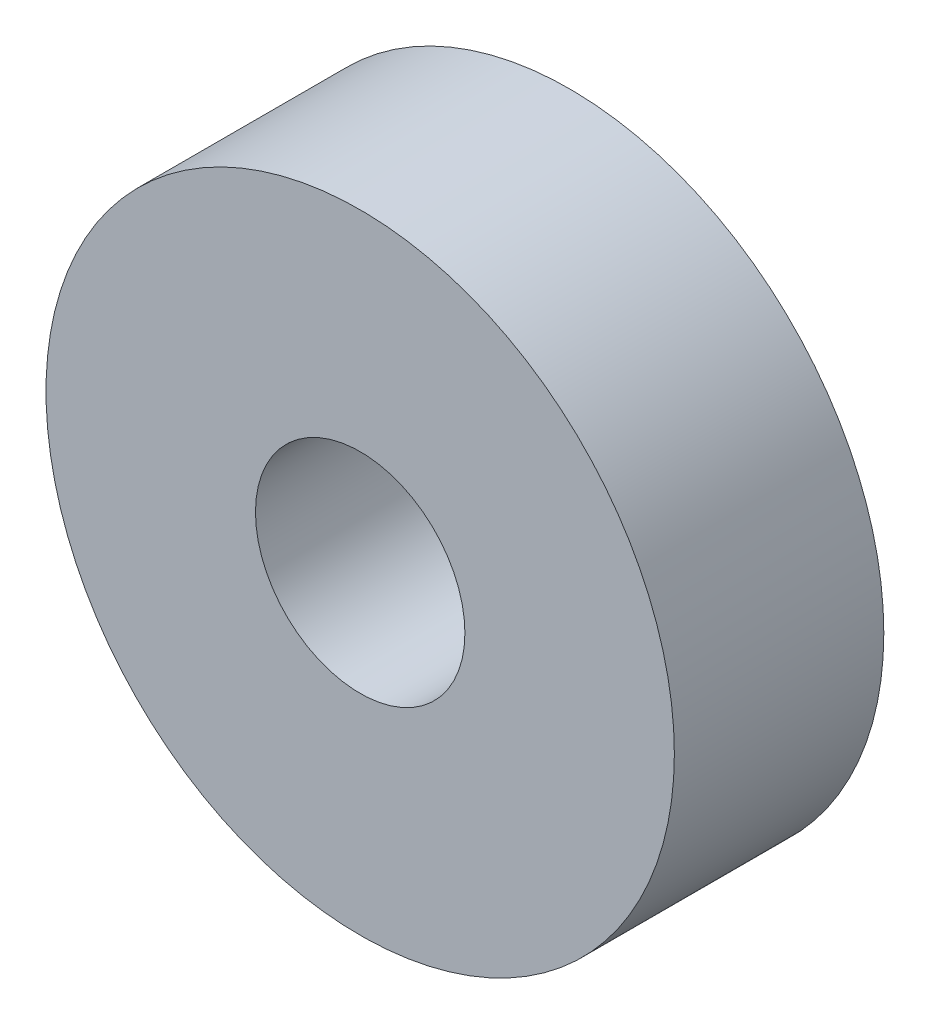
SolidWorks part; units mm, degrees
material "PA Type 6"
ref_plane "Front Plane" through (0, 0, 0) normal (0, 0, 1) x (1, 0, 0)
ref_plane "Top Plane" through (0, 0, 0) normal (0, 1, 0) x (1, 0, 0)
ref_plane "Right Plane" through (0, 0, 0) normal (1, 0, 0) x (0, 0, -1)
sketch "Sketch1" plane through (0, 0, 0) normal (0, 0, 1) x (1, 0, 0)
  circle A0 centre (0, 0) radius 2
  circle A1 centre (0, 0) radius 6
  dimension "D1" = 4
  dimension "D2" = 12
extrude "Boss-Extrude1" add sketch "Sketch1" along normal blind 4
